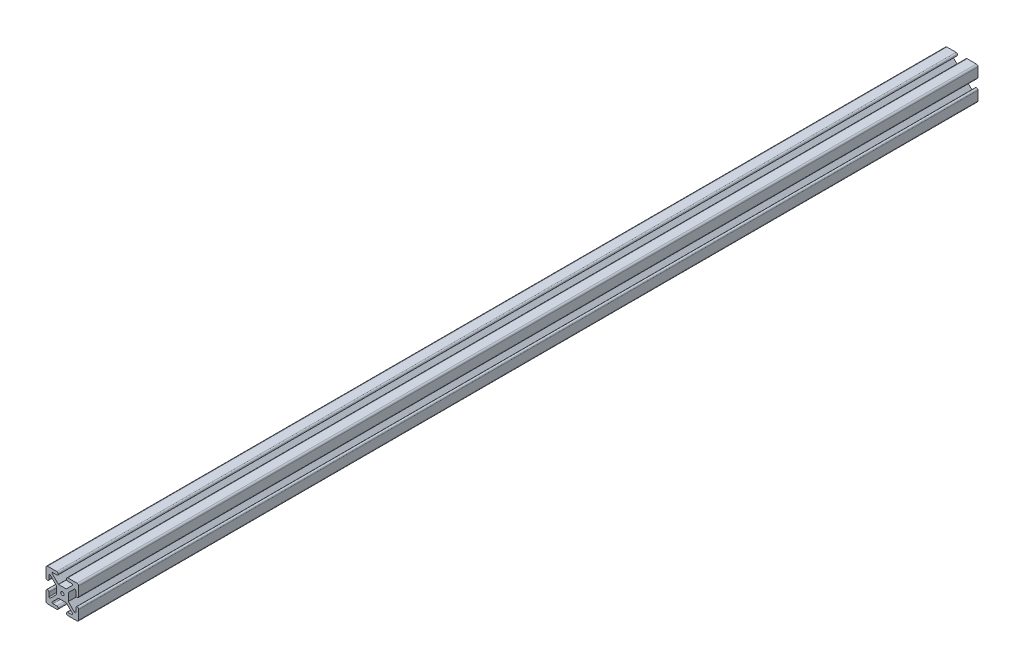
SolidWorks part; units mm, degrees
ref_plane "Front Plane" through (0, 0, 0) normal (0, 0, 1) x (1, 0, 0)
ref_plane "Top Plane" through (0, 0, 0) normal (0, 1, 0) x (1, 0, 0)
ref_plane "Right Plane" through (0, 0, 0) normal (1, 0, 0) x (0, 0, -1)
ref_plane "Plane1" through (0, 0, 50) normal (0, 0, 1) x (1, 0, 0)
sketch "Sketch1" plane through (0, 0, 50) normal (0, 0, 1) x (1, 0, 0)
  line L0 (-10, 9) -> (-10, 3.4)
  line L1 (-8.2, 3.4) -> (-8.2, 5.75)
  line L2 (-7.3464, 6.1036) -> (-3.656, 2.3842)
  line L3 (-3.65, 2.35) -> (-3.65, -2.35)
  line L4 (-3.656, -2.3842) -> (-7.3464, -6.1036)
  line L5 (-8.2, -5.75) -> (-8.2, -3.4)
  line L6 (-10, -3.4) -> (-10, -9)
  line L7 (-9, -10) -> (-3.4, -10)
  line L8 (-3.4, -8.2) -> (-5.75, -8.2)
  line L9 (-6.1036, -7.3464) -> (-2.444, -3.7158)
  line L10 (-2.35, -3.65) -> (2.35, -3.65)
  line L11 (2.444, -3.7158) -> (6.1036, -7.3464)
  line L12 (5.75, -8.2) -> (3.4, -8.2)
  line L13 (3.4, -10) -> (9, -10)
  line L14 (10, -9) -> (10, -3.4)
  line L15 (8.2, -3.4) -> (8.2, -5.75)
  line L16 (7.3464, -6.1036) -> (3.656, -2.3842)
  line L17 (3.65, -2.35) -> (3.65, 2.35)
  line L18 (3.656, 2.3842) -> (7.3464, 6.1036)
  line L19 (8.2, 5.75) -> (8.2, 3.4)
  line L20 (10, 3.4) -> (10, 9)
  line L21 (9, 10) -> (3.4, 10)
  line L22 (3.4, 8.2) -> (5.75, 8.2)
  line L23 (6.1036, 7.3464) -> (2.444, 3.7158)
  line L24 (2.35, 3.65) -> (-2.35, 3.65)
  line L25 (-2.444, 3.7158) -> (-6.1036, 7.3464)
  line L26 (-5.75, 8.2) -> (-3.4, 8.2)
  line L27 (-3.4, 10) -> (-9, 10)
  circle A0 centre (0, 0) radius 1
  arc A1 (-9, 10) -> (-10, 9) centre (-9, 9) ccw
  arc A2 (-10, 3.4) -> (-8.2, 3.4) centre (-9.1, 3.4) ccw
  arc A3 (-8.2, 5.75) -> (-7.3464, 6.1036) centre (-7.7, 5.75) cw
  arc A4 (-3.656, 2.3842) -> (-3.65, 2.35) centre (-3.75, 2.35) cw
  arc A5 (-3.65, -2.35) -> (-3.656, -2.3842) centre (-3.75, -2.35) cw
  arc A6 (-7.3464, -6.1036) -> (-8.2, -5.75) centre (-7.7, -5.75) cw
  arc A7 (-8.2, -3.4) -> (-10, -3.4) centre (-9.1, -3.4) ccw
  arc A8 (-10, -9) -> (-9, -10) centre (-9, -9) ccw
  arc A9 (-3.4, -10) -> (-3.4, -8.2) centre (-3.4, -9.1) ccw
  arc A10 (-5.75, -8.2) -> (-6.1036, -7.3464) centre (-5.75, -7.7) cw
  arc A11 (-2.444, -3.7158) -> (-2.35, -3.65) centre (-2.35, -3.75) cw
  arc A12 (2.35, -3.65) -> (2.444, -3.7158) centre (2.35, -3.75) cw
  arc A13 (6.1036, -7.3464) -> (5.75, -8.2) centre (5.75, -7.7) cw
  arc A14 (3.4, -8.2) -> (3.4, -10) centre (3.4, -9.1) ccw
  arc A15 (9, -10) -> (10, -9) centre (9, -9) ccw
  arc A16 (10, -3.4) -> (8.2, -3.4) centre (9.1, -3.4) ccw
  arc A17 (8.2, -5.75) -> (7.3464, -6.1036) centre (7.7, -5.75) cw
  arc A18 (3.656, -2.3842) -> (3.65, -2.35) centre (3.75, -2.35) cw
  arc A19 (3.65, 2.35) -> (3.656, 2.3842) centre (3.75, 2.35) cw
  arc A20 (7.3464, 6.1036) -> (8.2, 5.75) centre (7.7, 5.75) cw
  arc A21 (8.2, 3.4) -> (10, 3.4) centre (9.1, 3.4) ccw
  arc A22 (10, 9) -> (9, 10) centre (9, 9) ccw
  arc A23 (3.4, 10) -> (3.4, 8.2) centre (3.4, 9.1) ccw
  arc A24 (5.75, 8.2) -> (6.1036, 7.3464) centre (5.75, 7.7) cw
  arc A25 (2.444, 3.7158) -> (2.35, 3.65) centre (2.35, 3.75) cw
  arc A26 (-2.35, 3.65) -> (-2.444, 3.7158) centre (-2.35, 3.75) cw
  arc A27 (-6.1036, 7.3464) -> (-5.75, 8.2) centre (-5.75, 7.7) cw
  arc A28 (-3.4, 8.2) -> (-3.4, 10) centre (-3.4, 9.1) ccw
extrude "Boss-Extrude1" add sketch "Sketch1" against normal blind 550
